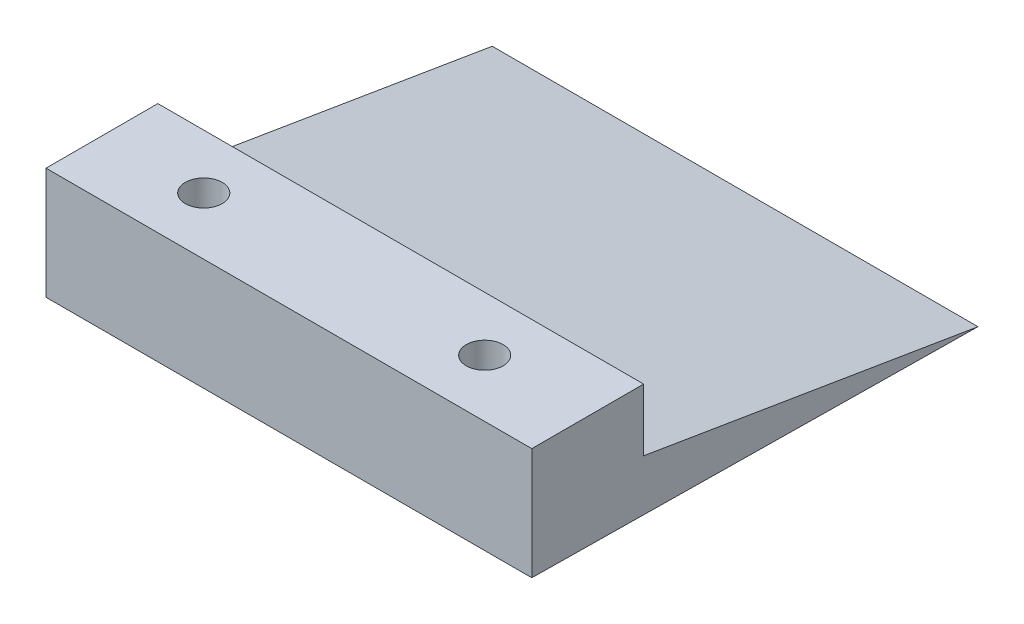
SolidWorks part; units mm, degrees
material "2024 Alloy"
ref_plane "Front Plane" through (0, 0, 0) normal (0, 0, 1) x (1, 0, 0)
ref_plane "Top Plane" through (0, 0, 0) normal (0, 1, 0) x (1, 0, 0)
ref_plane "Right Plane" through (0, 0, 0) normal (1, 0, 0) x (0, 0, -1)
sketch "Sketch2" plane through (0, 0, 0) normal (1, 0, 0) x (0, 0, -1)
  line L0 (0, 0) -> (29.5968, -4.9019)
  line L1 (-9.9, 5.5) -> (0, 5.5)
  line L2 (-9.9, 5.5) -> (-9.9, -4.4)
  line L4 (0, 5.5) -> (0, 0)
  line L5 (29.5968, -4.9019) -> (-9.9, -4.4)
  dimension "D1" = 9.9
  dimension "D2" = 9.9
  dimension "D3" = 39.5
  dimension "D4" = 5.5
  dimension "D5" = 30
extrude "Boss-Extrude1" add sketch "Sketch2" along normal mid plane 43
sketch "Sketch4" plane through (0, 5.5, 0) normal (0, 1, 0) x (1, 0, 0)
  line L0 (-21.5, 0) -> (-21.5, -9.9) construction
  circle A0 centre (-12.615, -4.95) radius 0.685
  circle A1 centre (12.255, -4.95) radius 0.685
  point P5 (-21.5, -4.95)
  dimension "D1" = 1.37
  dimension "D3" = 8.2
  dimension "D2" = 24.87
extrude "Cut-Extrude1" cut sketch "Sketch4" against normal through all
hole_wizard "CBORE for #4 Socket Head Cap Screw1" positions "Sketch5" profile "Sketch6" counterbore size "#4" standard "ANSI Inch" end condition through all
sketch "Sketch5" plane through (0, -4.5251, 0.0575) normal (0, -0.9999, 0.0127) x (-1, 0, 0)
  point P0 (12.615, -4.8929)
  point P2 (-12.255, -4.8929)
sketch "Sketch6" plane through (-12.615, -4.4629, 4.95) normal (1, 0, 0) x (0, -0.0127, -0.9999)
  line L0 (0, 0) -> (0, 10.4011)
  line L1 (0, 10.4011) -> (1.6319, 10.4011)
  line L3 (1.6319, 10.4011) -> (1.6319, 6.8448)
  line L4 (1.6319, 6.8448) -> (2.7788, 6.8448)
  line L5 (2.7788, 6.8448) -> (2.7788, 0)
  line L7 (2.7788, 0) -> (0, 0)
  line L11 (0, -6.35) -> (0, 107.95) construction
  dimension "Thru Hole Dia." = 3.2639
  dimension "Thru Hole Depth" = 10.4011
  dimension "C'Bore Dia." = 5.5575
  dimension "C'Bore Depth" = 6.8448
